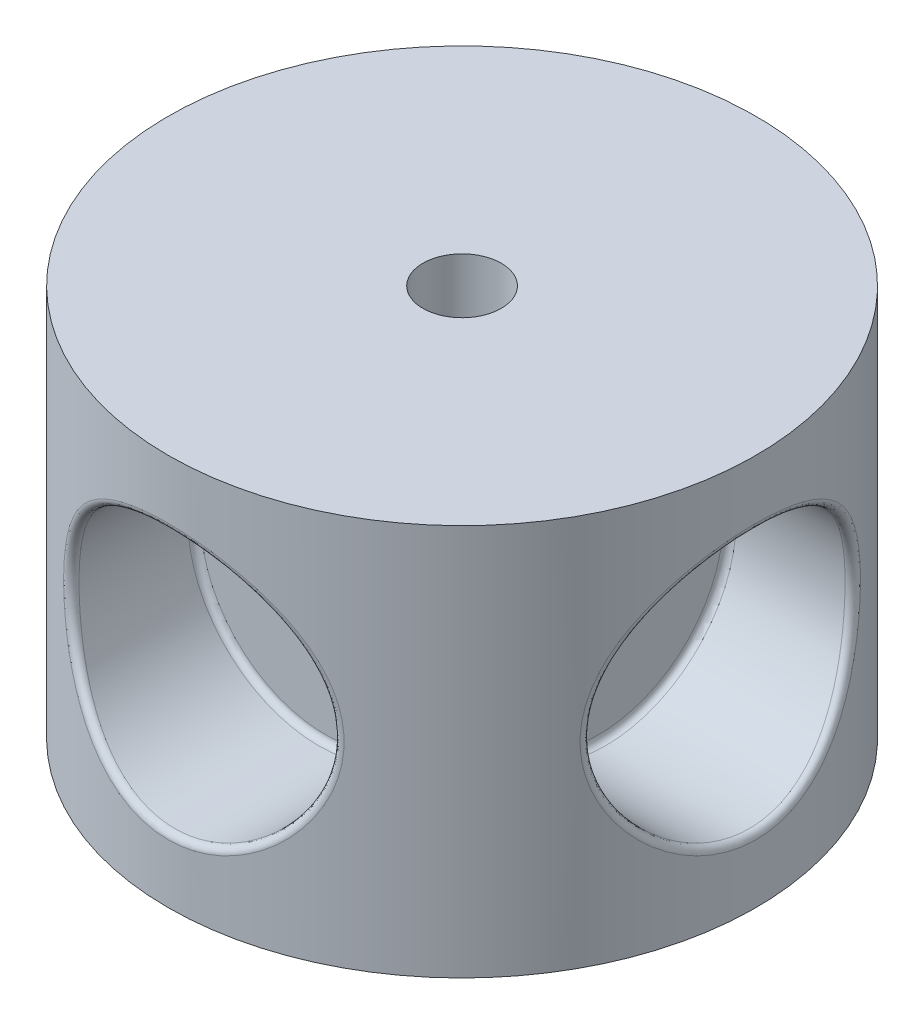
SolidWorks part; units mm, degrees
ref_plane "Alzado" through (0, 0, 0) normal (0, 0, 1) x (1, 0, 0)
ref_plane "Planta" through (0, 0, 0) normal (0, 1, 0) x (1, 0, 0)
ref_plane "Vista lateral" through (0, 0, 0) normal (1, 0, 0) x (0, 0, -1)
sketch "Croquis1" plane through (0, 0, 0) normal (0, 1, 0) x (1, 0, 0)
  circle A0 centre (0, 0) radius 22.5
  dimension "D1" = 45
extrude "Saliente-Extruir1" add sketch "Croquis1" along normal blind 30
ref_plane "Plano1" through (0, 0, 0) normal (0, -1, 0) x (-1, 0, 0)
ref_axis "Eje1" through (0, 30, 0) along (0, -1, 0)
sketch "Croquis2" plane through (0, 0, 0) normal (0, -1, 0) x (-1, 0, 0)
  line L0 (0, 0) -> (30.1607, 0) construction
ref_plane "Plano2" through (-22.5, 0, 0) normal (-1, 0, 0) x (0, 0, 1)
sketch "Croquis3" plane through (-22.5, 0, 0) normal (-1, 0, 0) x (0, 0, 1)
  line L0 (0, 30) -> (0, 0) construction
  line L1 (22.5, 30) -> (-22.5, 30) construction
  circle A0 centre (0, 15) radius 10
  dimension "D1" = 20
  dimension "D2" = 15
extrude "Cortar-Extruir1" cut sketch "Croquis3" against normal blind 12
fillet "Redondeo1" radius 0.5 2 edges at (-20.1974, 16.2982, -9.9154) (-10.5, 15, 10)
pattern_circular "MatrizC4" count 4 over 360 about axis through (0, 30, 0) along (0, -1, 0) of "Redondeo1", "Cortar-Extruir1"
sketch "Croquis4" plane through (0, 0, 0) normal (0, -1, 0) x (1, 0, 0)
  circle A0 centre (0, 0) radius 3
  dimension "D1" = 6
extrude "Cortar-Extruir2" cut sketch "Croquis4" against normal blind 30 contours A0
sketch "Croquis5" plane through (0, 0, 0) normal (0, -1, 0) x (1, 0, 0)
  line L1 (-7.5, 1) -> (7.5, 1)
  line L2 (-7.5, 1) -> (-7.5, -1)
  line L3 (-7.5, -1) -> (7.5, -1)
  line L4 (7.5, 1) -> (7.5, -1)
  line L5 (-7.5, 1) -> (7.5, -1) construction
  line L6 (-7.5, -1) -> (7.5, 1) construction
  point P0 (0, 0)
  dimension "D1" = 15
  dimension "D2" = 2
extrude "Cortar-Extruir3" cut sketch "Croquis5" against normal blind 5
sketch "Croquis6" plane through (0, 30, 0) normal (0, 1, 0) x (1, 0, 0)
  line L0 (0, 0) -> (-0.712, 0.712)
  line L1 (0, 0) -> (22.5, 0)
  line L2 (0, 0) -> (0, -22.5)
  line L3 (0, 0) -> (-22.5, 0)
  line L4 (0, 0) -> (0, 22.5)
  circle A0 centre (0, 0) radius 22.5 construction
  point P13 (0, 0)
  dimension "D1" = 4
